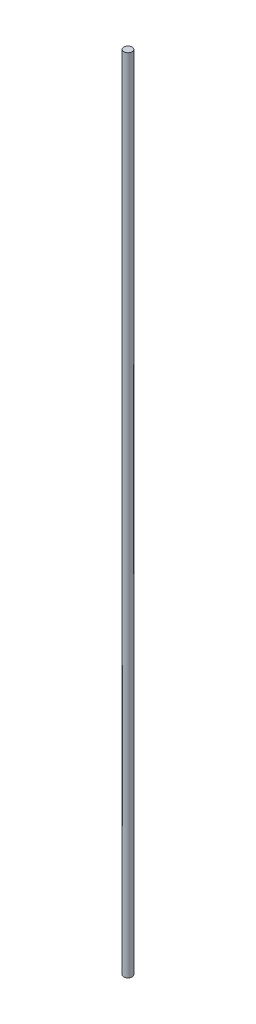
SolidWorks part; units mm, degrees
material "Liga 1060"
ref_plane "Plano frontal" through (0, 0, 0) normal (0, 0, 1) x (1, 0, 0)
ref_plane "Plano superior" through (0, 0, 0) normal (0, 1, 0) x (1, 0, 0)
ref_plane "Plano direito" through (0, 0, 0) normal (1, 0, 0) x (0, 0, -1)
sketch "Esboço1" plane through (0, 0, 0) normal (0, 1, 0) x (1, 0, 0)
  circle A0 centre (0, 0) radius 3.97
  dimension "D1" = 7.94
extrude "Ressalto-extrusão1" add sketch "Esboço1" along normal mid plane 768
